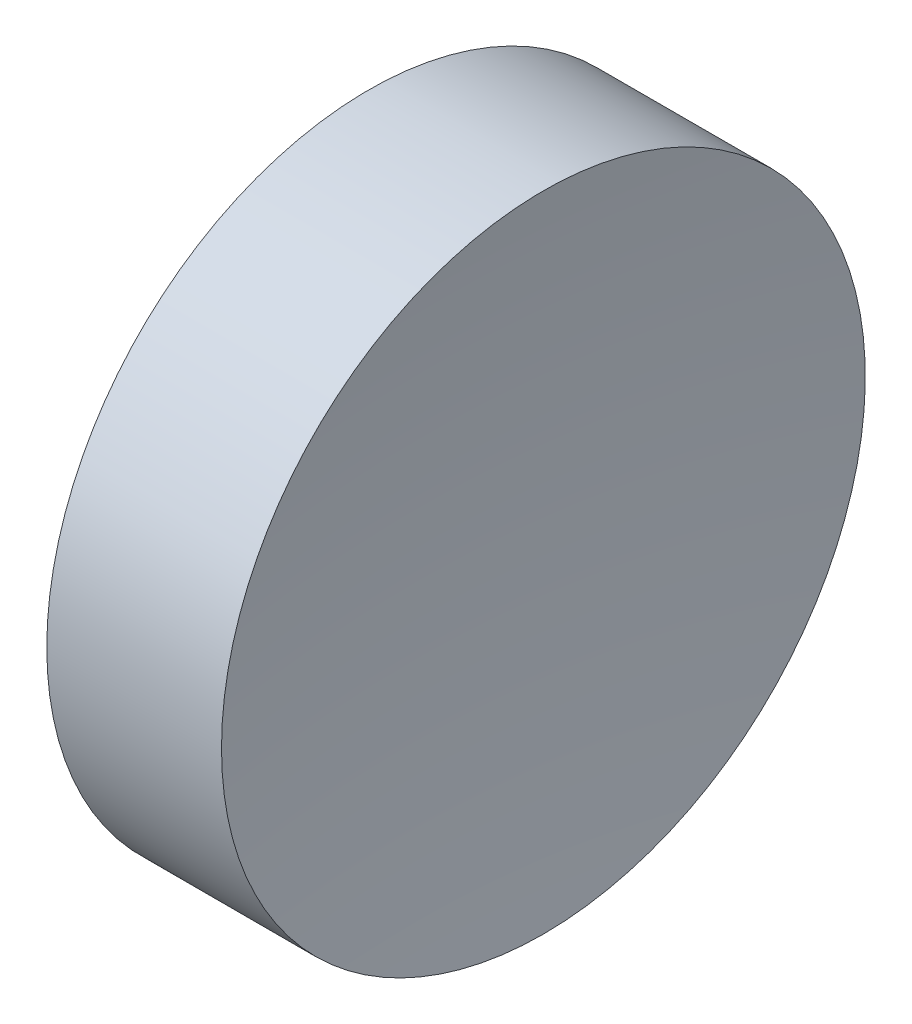
SolidWorks part; units mm, degrees
ref_plane "前视基准面" through (0, 0, 0) normal (0, 0, 1) x (1, 0, 0)
ref_plane "上视基准面" through (0, 0, 0) normal (0, 1, 0) x (1, 0, 0)
ref_plane "右视基准面" through (0, 0, 0) normal (1, 0, 0) x (0, 0, -1)
sketch "草图1" plane through (0, 0, 0) normal (0, 0, 1) x (1, 0, 0)
  line L0 (108.9851, 69.378) -> (132.7763, 69.378) construction
  line L1 (115.0927, 69.378) -> (115.0927, 81.878)
  line L2 (115.0927, 81.878) -> (121.877, 81.878)
  line L3 (121.0927, 69.378) -> (115.0927, 69.378)
  arc A0 (121.877, 81.878) -> (121.0927, 69.378) centre (221.0927, 69.378) ccw
revolve "旋转1" add sketch "草图1" angle 360 about L0
